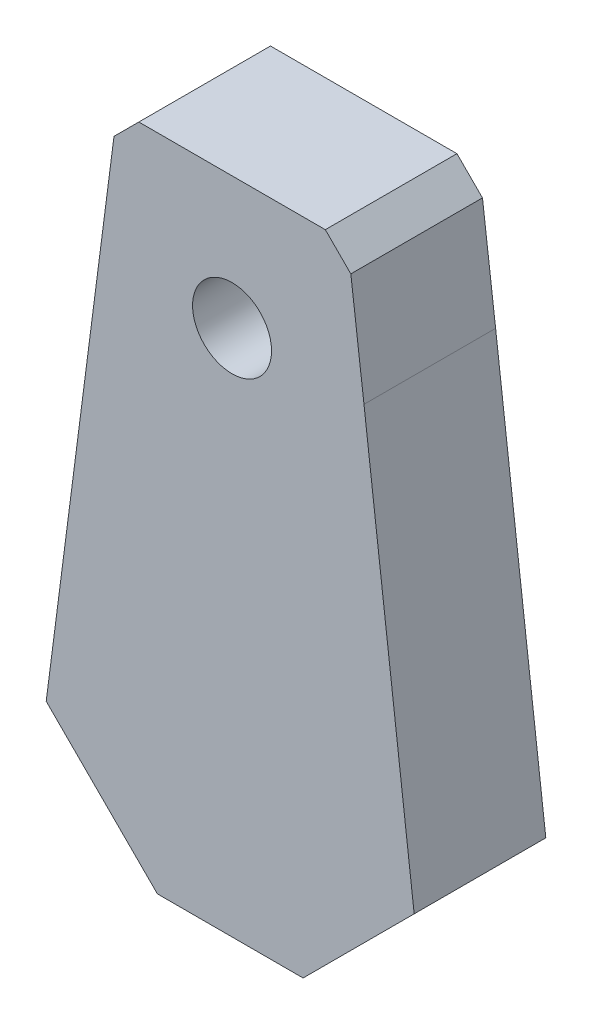
SolidWorks part; units mm, degrees
ref_plane "Plano frontal" through (0, 0, 0) normal (0, 0, 1) x (1, 0, 0)
ref_plane "Plano superior" through (0, 0, 0) normal (0, 1, 0) x (1, 0, 0)
ref_plane "Plano direito" through (0, 0, 0) normal (1, 0, 0) x (0, 0, -1)
sketch "Model" plane through (0, 0, 0) normal (0, 0, 1) x (1, 0, 0)
  line L0 (36.6764, 11.5591) -> (43.3183, 11.5591)
  line L1 (31.6082, 16.6273) -> (36.6764, 11.5591)
  line L2 (34.6989, 40.4736) -> (35.831, 41.6057)
  line L3 (46.0932, 35.5922) -> (45.4943, 40.4423)
  line L4 (44.331, 41.6057) -> (45.4943, 40.4423)
  line L5 (48.3812, 16.622) -> (46.0932, 35.5922)
  line L6 (44.331, 41.6057) -> (35.831, 41.6057)
  line L7 (43.3183, 11.5591) -> (48.3812, 16.622)
  line L8 (31.6082, 16.6273) -> (34.6989, 40.4736)
  circle A0 centre (40.0797, 35.5922) radius 1.8
extrude "Ressalto-extrusão1" add sketch "Model" along normal blind 6
